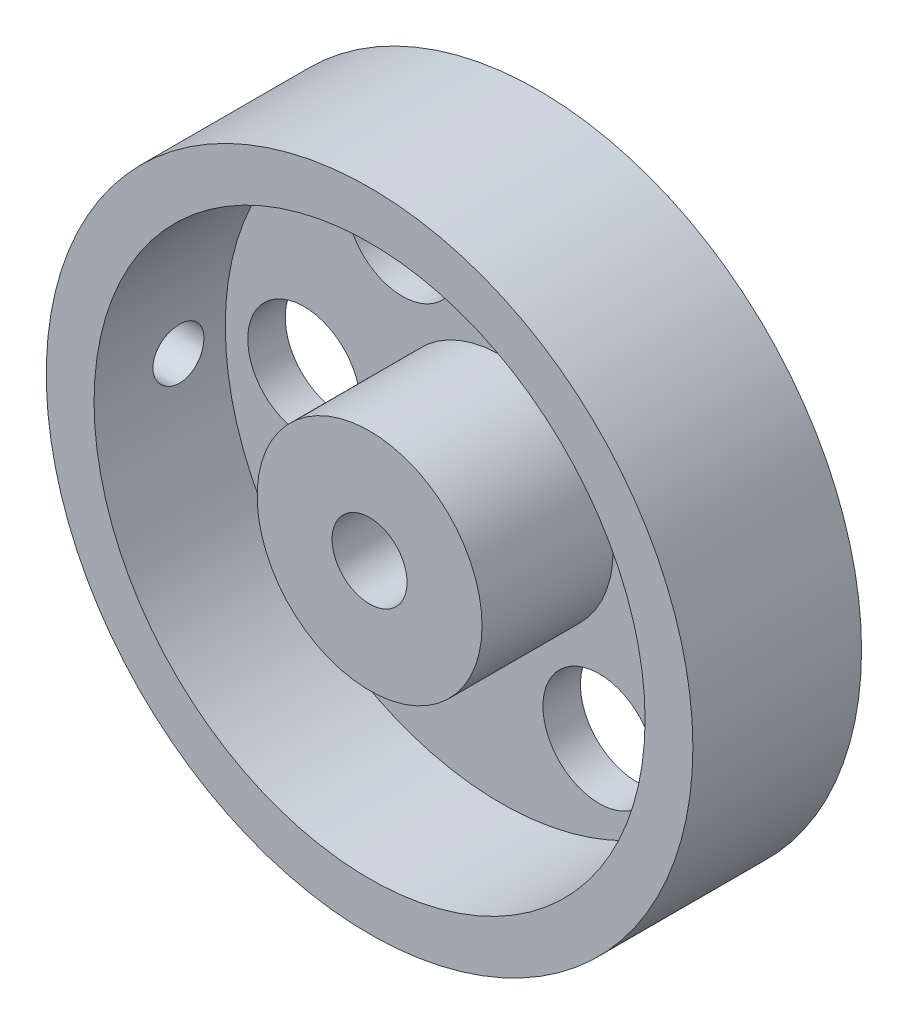
SolidWorks part; units mm, degrees
ref_plane "Front Plane" through (0, 0, 0) normal (0, 0, 1) x (1, 0, 0)
ref_plane "Top Plane" through (0, 0, 0) normal (0, 1, 0) x (1, 0, 0)
ref_plane "Right Plane" through (0, 0, 0) normal (1, 0, 0) x (0, 0, -1)
sketch "Sketch1" plane through (0, 0, 0) normal (0, 0, 1) x (1, 0, 0)
  circle A0 centre (0, 0) radius 17.25
extrude "Boss-Extrude1" add sketch "Sketch1" along normal mid plane 9
sketch "Sketch2" plane through (0, 0, 4.5) normal (0, 0, 1) x (1, 0, 0)
  circle A0 centre (0, 0) radius 2
extrude "Cut-Extrude1" cut sketch "Sketch2" against normal blind 9
sketch "Sketch3" plane through (0, 0, 4.5) normal (0, 0, 1) x (1, 0, 0)
  circle A0 centre (0, 0) radius 6
  circle A1 centre (0, 0) radius 14.7
extrude "Cut-Extrude2" cut sketch "Sketch3" against normal blind 7
sketch "Sketch4" plane through (0, 0, -2.5) normal (0, 0, 1) x (1, 0, 0)
  circle A0 centre (10.5, 0) radius 3
  circle A1 centre (5.25, -9.0933) radius 3
  circle A2 centre (-5.25, -9.0933) radius 3
  circle A3 centre (-10.5, 0) radius 3
  circle A4 centre (-5.25, 9.0933) radius 3
  circle A5 centre (5.25, 9.0933) radius 3
  point P16 (0, 0)
  dimension "D1" = 6
extrude "Cut-Extrude3" cut sketch "Sketch4" against normal up to next
sketch "Sketch5" plane through (0, 0, 0) normal (1, 0, 0) x (0, 0, -1)
  circle A0 centre (0, 0) radius 1.3593
extrude "Cut-Extrude4" cut sketch "Sketch5" against normal blind 18
